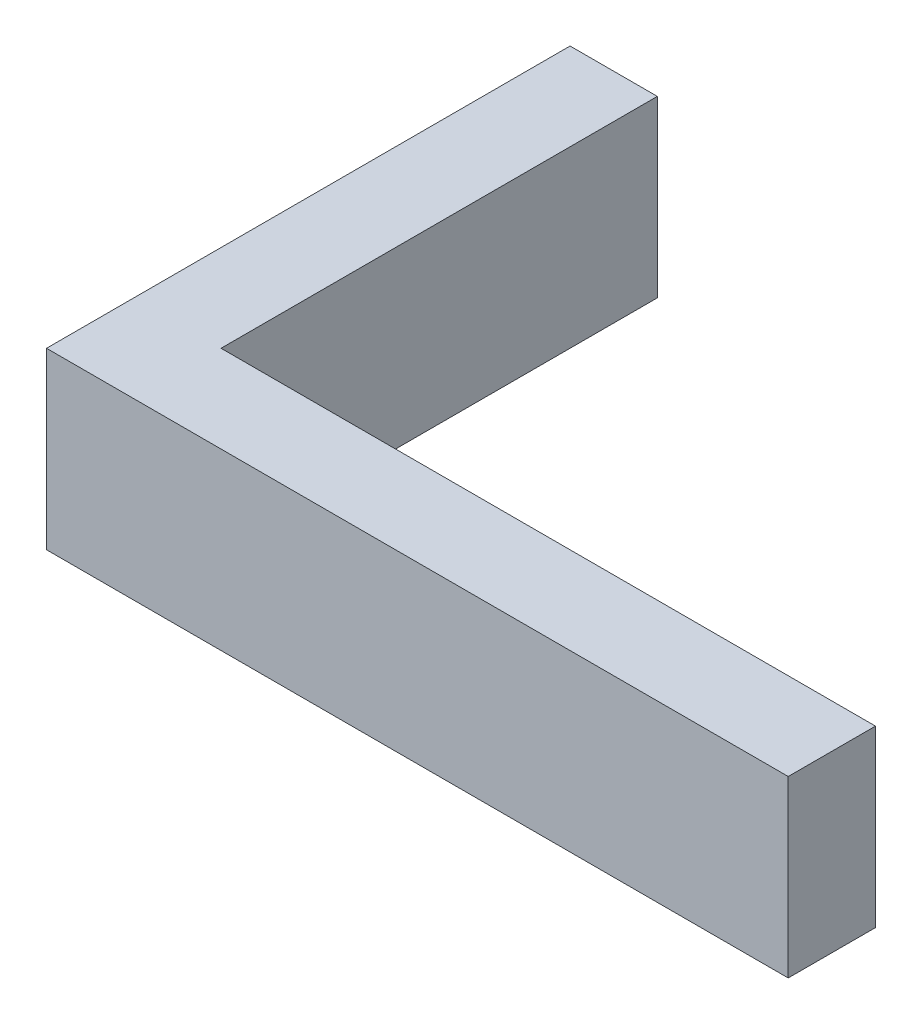
SolidWorks part; units mm, degrees
ref_plane "Front Plane" through (0, 0, 0) normal (0, 0, 1) x (1, 0, 0)
ref_plane "Top Plane" through (0, 0, 0) normal (0, 1, 0) x (1, 0, 0)
ref_plane "Right Plane" through (0, 0, 0) normal (1, 0, 0) x (0, 0, -1)
sketch "Sketch2" plane through (0, 0, 0) normal (0, 1, 0) x (1, 0, 0)
  line L10 (-12.7317, 5) -> (-12.7317, -7)
  line L11 (-12.7317, -7) -> (4.2683, -7)
  line L12 (4.2683, -7) -> (4.2683, -5)
  line L13 (4.2683, -5) -> (-10.7317, -5)
  line L14 (-10.7317, -5) -> (-10.7317, 5)
  line L15 (-10.7317, 5) -> (-12.7317, 5)
  dimension "D1" = 2
  dimension "D2" = 10
  dimension "D3" = 2
  dimension "D4" = 15
extrude "Boss-Extrude1" add sketch "Sketch2" along normal blind 4
